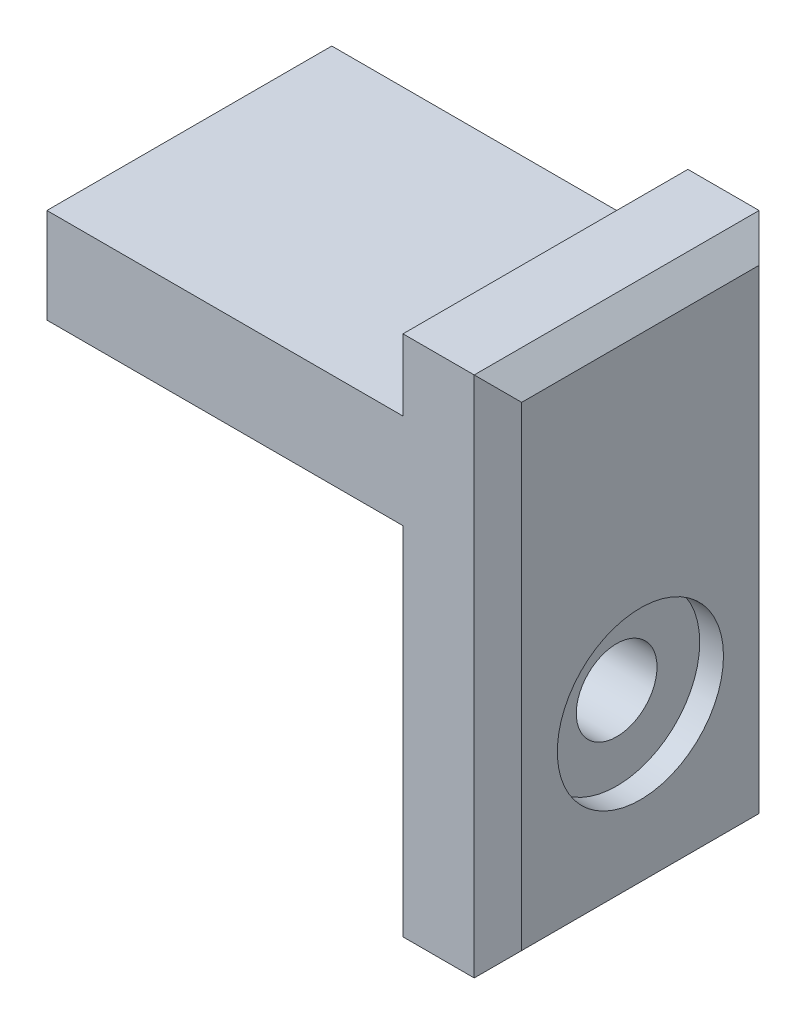
SolidWorks part; units mm, degrees
ref_plane "Front Plane" through (0, 0, 0) normal (0, 0, 1) x (1, 0, 0)
ref_plane "Top Plane" through (0, 0, 0) normal (0, 1, 0) x (1, 0, 0)
ref_plane "Right Plane" through (0, 0, 0) normal (1, 0, 0) x (0, 0, -1)
sketch "Sketch1" plane through (0, 0, 0) normal (0, 0, 1) x (1, 0, 0)
  line L0 (0, 19) -> (15, 19)
  line L1 (15, 0) -> (19, 0)
  line L2 (0, 15) -> (0, 19)
  line L3 (0, 15) -> (15, 15)
  line L4 (15, 0) -> (15, 15)
  line L5 (19, 0) -> (19, 19)
  line L6 (19, 19) -> (19, 22)
  line L7 (19, 22) -> (15, 22)
  line L8 (15, 22) -> (15, 19)
  line L9 (0, 19) -> (19, 19) construction
  dimension "D1" = 15
  dimension "D2" = 15
  dimension "D4" = 3
  dimension "D3" = 4
extrude "Boss-Extrude1" add sketch "Sketch1" along normal blind 12
sketch "Sketch2" plane through (15, 0, 0) normal (-1, 0, 0) x (0, 0, 1)
  line L0 (0, 15) -> (0, 0) construction
  line L1 (12, 0) -> (0, 0) construction
  circle A0 centre (6, 7.5) radius 1.7
  dimension "D1" = 3.4
  dimension "D2" = 6
  dimension "D3" = 7.5
extrude "Cut-Extrude1" cut sketch "Sketch2" against normal blind 12
sketch "Sketch3" plane through (19, 0, 0) normal (1, 0, 0) x (0, 0, -1)
  circle A0 centre (-6, 7.5) radius 3.5
  dimension "D1" = 7
extrude "Cut-Extrude2" cut sketch "Sketch3" against normal blind 1
chamfer "Chamfer1" distance 1 angle 45 4 edges at (19, 22, 6) (19, 11, 0) (19, 0, 6) (19, 11, 12)
